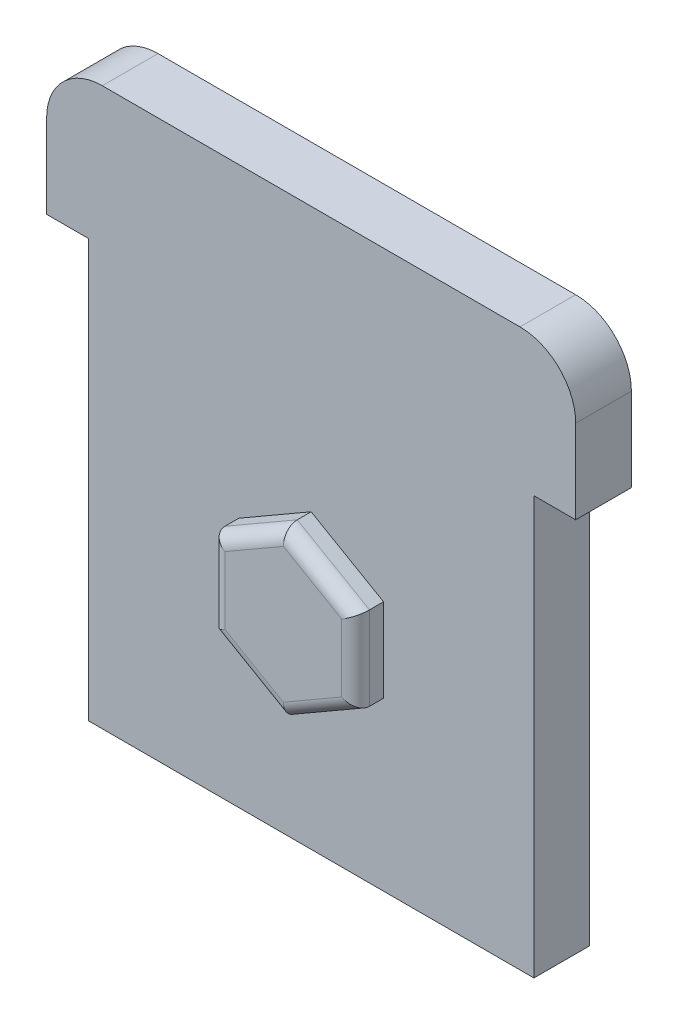
SolidWorks part; units mm, degrees
ref_plane "Alzado" through (0, 0, 0) normal (0, 0, 1) x (1, 0, 0)
ref_plane "Planta" through (0, 0, 0) normal (0, 1, 0) x (1, 0, 0)
ref_plane "Vista lateral" through (0, 0, 0) normal (1, 0, 0) x (0, 0, -1)
sketch "Croquis1" plane through (0, 0, 0) normal (0, 0, 1) x (1, 0, 0)
  line L0 (0, 0) -> (-1.5, 0) construction
  line L1 (0, 0) -> (16, 0)
  line L2 (0, 0) -> (0, -15)
  line L3 (0, -15) -> (16, -15)
  line L4 (16, 0) -> (16, -15)
  line L6 (-1.5, 0) -> (17.5, 0)
  line L7 (-1.5, 0) -> (-1.5, 5)
  line L8 (-1.5, 5) -> (17.5, 5)
  line L9 (17.5, 0) -> (17.5, 5)
  dimension "D1" = 16
  dimension "D2" = 15
  dimension "D3" = 1.5
  dimension "D4" = 19
  dimension "D5" = 5
extrude "Saliente-Extruir3" add sketch "Croquis1" along normal blind 2 contours L6 L9 L8 L7 L1 | L4 L1 L2 L3
fillet "Redondeo1" radius 2 2 edges at (-1.5, 5, 1) (17.5, 5, 1)
sketch "Croquis3" plane through (0, 0, 2) normal (0, 0, 1) x (1, 0, 0)
  line L0 (0, 0) -> (16, -15) construction
  line L1 (16, -15) -> (0, -15) construction
  line L2 (0, -15) -> (16, 0) construction
  line L4 (8, -4.5) -> (5.4019, -6)
  line L5 (5.4019, -6) -> (5.4019, -9)
  line L6 (5.4019, -9) -> (8, -10.5)
  line L7 (8, -10.5) -> (10.5981, -9)
  line L8 (10.5981, -9) -> (10.5981, -6)
  line L9 (10.5981, -6) -> (8, -4.5)
  circle A0 centre (8, -7.5) radius 2.5981 construction
  dimension "D1" = 3
extrude "Saliente-Extruir4" add sketch "Croquis3" along normal blind 1
fillet "Redondeo2" radius 0.5 6 edges at (10.5981, -7.5, 3) (9.299, -9.75, 3) (6.701, -9.75, 3) (5.4019, -7.5, 3) (6.701, -5.25, 3) (9.299, -5.25, 3)
